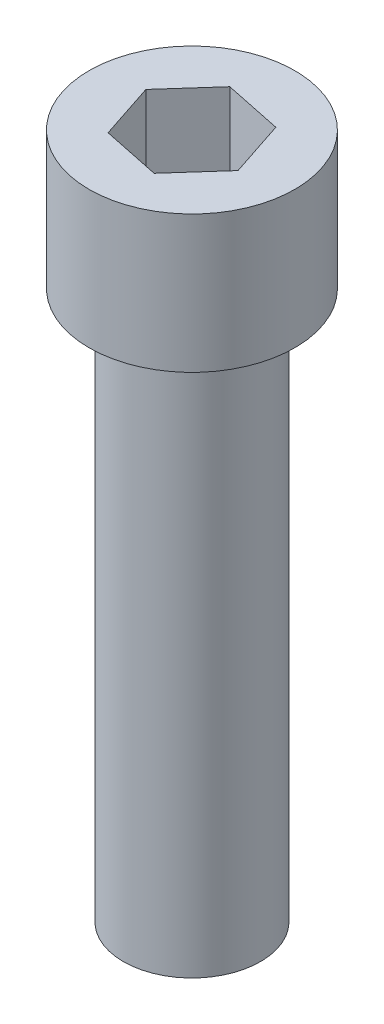
SolidWorks part; units mm, degrees
ref_plane "Front Plane" through (0, 0, 0) normal (0, 0, 1) x (1, 0, 0)
ref_plane "Top Plane" through (0, 0, 0) normal (0, 1, 0) x (1, 0, 0)
ref_plane "Right Plane" through (0, 0, 0) normal (1, 0, 0) x (0, 0, -1)
sketch "Sketch1" plane through (0, 0, 0) normal (0, 1, 0) x (1, 0, 0)
  circle A0 centre (0, 0) radius 3.175
extrude "Boss-Extrude1" add sketch "Sketch1" along normal blind 25.4
sketch "Sketch2" plane through (0, 25.4, 0) normal (0, 1, 0) x (1, 0, 0)
  circle A0 centre (0, 0) radius 4.7625
extrude "Boss-Extrude2" add sketch "Sketch2" along normal blind 6.35
sketch "Sketch3" plane through (0, 31.75, 0) normal (0, 1, 0) x (1, 0, 0)
  line L1 (-2.692, 0.5599) -> (-1.8309, -2.0514)
  line L2 (-1.8309, -2.0514) -> (0.8611, -2.6113)
  line L3 (0.8611, -2.6113) -> (2.692, -0.5599)
  line L4 (2.692, -0.5599) -> (1.8309, 2.0514)
  line L5 (1.8309, 2.0514) -> (-0.8611, 2.6113)
  line L6 (-0.8611, 2.6113) -> (-2.692, 0.5599)
  circle A0 centre (0, 0) radius 2.3812 construction
extrude "Cut-Extrude1" cut sketch "Sketch3" against normal blind 6.35
